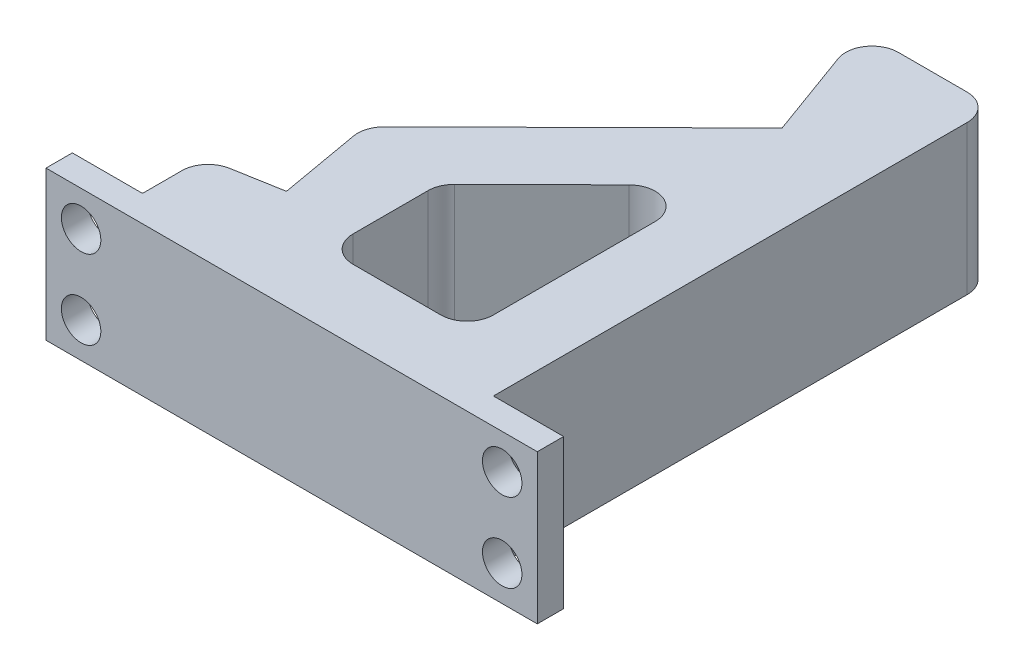
SolidWorks part; units mm, degrees
ref_plane "Front Plane" through (0, 0, 0) normal (0, 0, 1) x (1, 0, 0)
ref_plane "Top Plane" through (0, 0, 0) normal (0, 1, 0) x (1, 0, 0)
ref_plane "Right Plane" through (0, 0, 0) normal (1, 0, 0) x (0, 0, -1)
sketch "Sketch1" plane through (0, 0, 0) normal (0, 1, 0) x (1, 0, 0)
  line L0 (0, 0) -> (0, 10)
  line L1 (0, 0) -> (40, 0)
  line L2 (40, 0) -> (40, 60)
  line L3 (40, 60) -> (24.8697, 60)
  line L4 (24.8697, 60) -> (30, 45.9046)
  line L6 (30, 45.9046) -> (6.0899, 22.2435)
  line L7 (6.0899, 22.2435) -> (8, 11.4106)
  line L8 (8, 11.4106) -> (0, 10)
  line L9 (16, 8) -> (32, 8)
  line L10 (32, 8) -> (32, 36.6288)
  line L11 (32, 36.6288) -> (16, 20.7955)
  line L12 (16, 20.7955) -> (16, 8)
  dimension "D1" = 40
  dimension "D2" = 60
  dimension "D3" = 70
  dimension "D4" = 100
  dimension "D5" = 10
  dimension "D6" = 11
  dimension "D7" = 15
  dimension "D8" = 10
  dimension "D9" = 8
  dimension "D10" = 8
  dimension "D11" = 8
  dimension "D12" = 8
  dimension "D13" = 8
extrude "Boss-Extrude1" add sketch "Sketch1" along normal mid plane 17 contours L1 L2 L3 L4 L6 L7 L8 L0
fillet "Fillet1" radius 3 8 edges at (40, 0, -60) (16, 0, -8) (16, 0, -20.7955) (32, 0, -36.6288) (32, 0, -8) (0, 0, -10) (6.0899, 0, -22.2435) (24.8697, 0, -60)
sketch "Sketch2" plane through (0, 8.5, 0) normal (0, 1, 0) x (1, 0, 0)
  line L1 (0, 0) -> (-8, 0)
  line L2 (0, 0) -> (0, 3)
  line L3 (0, 3) -> (-8, 3)
  line L4 (-8, 0) -> (-8, 3)
  line L5 (40, 0) -> (48, 0)
  line L6 (40, 0) -> (40, 3)
  line L7 (40, 3) -> (48, 3)
  line L8 (48, 0) -> (48, 3)
  dimension "D1" = 3
  dimension "D2" = 8
  dimension "D3" = 8
extrude "Boss-Extrude2" add sketch "Sketch2" against normal up to surface (17 mm away) up to face at (18.7706, -8.5, -29.5137)
sketch "Sketch3" plane through (0, 0, -3) normal (0, 0, -1) x (-1, 0, 0)
  line L0 (0, 8.5) -> (8, 8.5) construction
  line L1 (8, -8.5) -> (0, -8.5) construction
  line L2 (-40, -8.5) -> (-40, 8.5) construction
  line L3 (0, -8.5) -> (0, 8.5) construction
  circle A0 centre (4, -4.5) radius 2.25
  circle A1 centre (4, 4.5) radius 2.25
  circle A2 centre (-44, 4.5) radius 2.25
  circle A3 centre (-44, -4.5) radius 2.25
  dimension "D1" = 4.5
  dimension "D2" = 4.5
  dimension "D3" = 4.5
  dimension "D4" = 4.5
  dimension "D5" = 4
  dimension "D6" = 4
  dimension "D7" = 4
  dimension "D8" = 4
extrude "Cut-Extrude1" cut sketch "Sketch3" against normal through all
